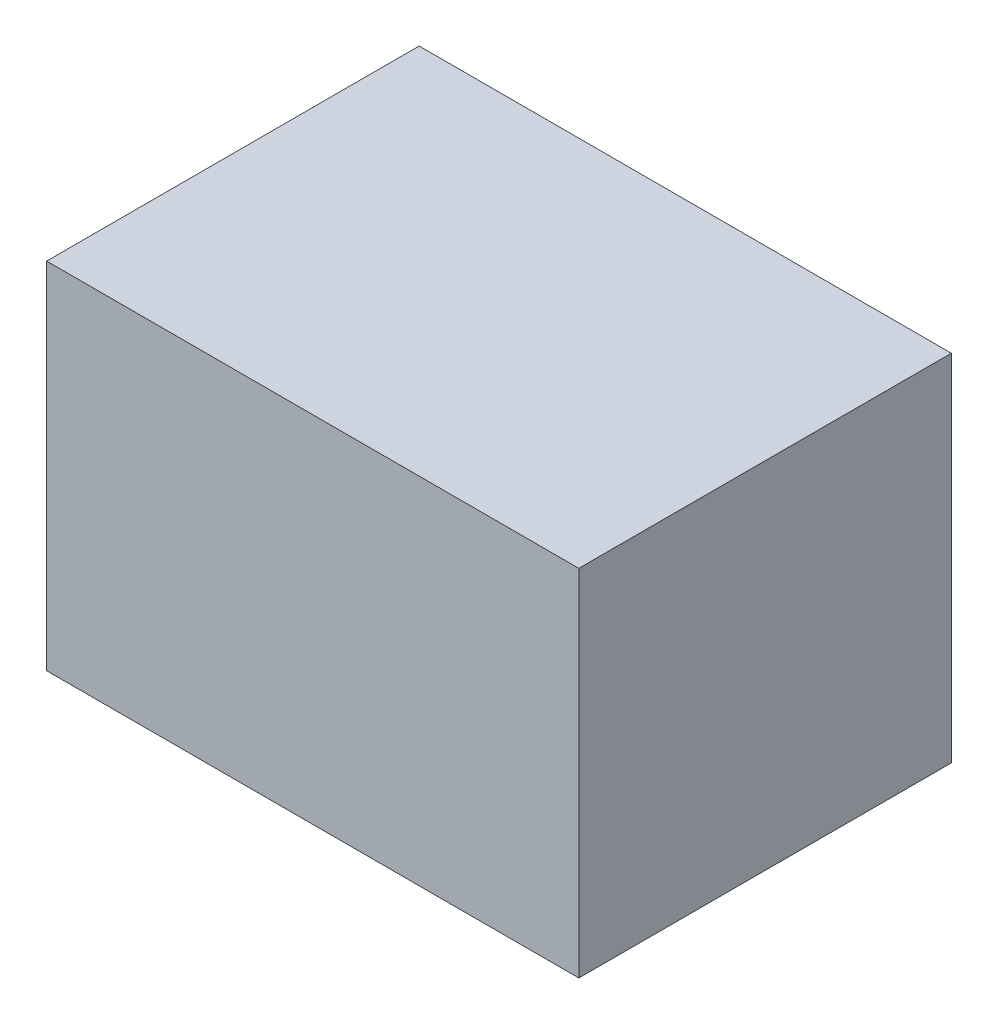
SolidWorks part; units mm, degrees
ref_plane "Front Plane" through (0, 0, 0) normal (0, 0, 1) x (1, 0, 0)
ref_plane "Top Plane" through (0, 0, 0) normal (0, 1, 0) x (1, 0, 0)
ref_plane "Right Plane" through (0, 0, 0) normal (1, 0, 0) x (0, 0, -1)
sketch "Sketch1" plane through (0, 0, 0) normal (0, 0, 1) x (1, 0, 0)
  line L1 (0, 0) -> (152.4, 0)
  line L2 (0, 0) -> (0, 101.6)
  line L3 (0, 101.6) -> (152.4, 101.6)
  line L4 (152.4, 0) -> (152.4, 101.6)
  dimension "D1" = 152.4
  dimension "D2" = 101.6
extrude "Boss-Extrude1" add sketch "Sketch1" along normal blind 101.6 and the other way blind 5.08
sketch "Sketch2" plane through (0, 0, -5.08) normal (0, 0, -1) x (-1, 0, 0)
  circle A0 centre (-76.2, 50.8) radius 12.954
extrude "Cut-Extrude1" cut sketch "Sketch2" against normal blind 101.6
sketch3d "URDF Reference"
  line L0 (0, 0, 0) -> (10, 0, 0) construction
  line L1 (0, 0, 0) -> (0, 0, -10) construction
  point P0 (0, 0, 0)
